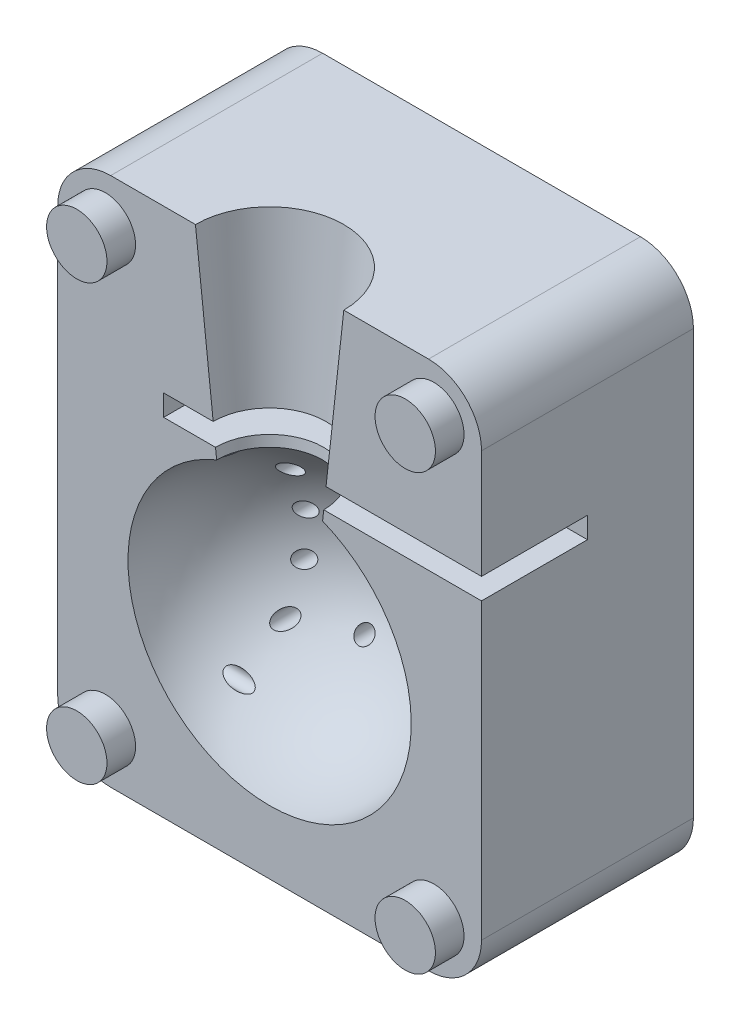
SolidWorks part; units mm, degrees
ref_plane "Alzado" through (0, 0, 0) normal (0, 0, 1) x (1, 0, 0)
ref_plane "Planta" through (0, 0, 0) normal (0, 1, 0) x (1, 0, 0)
ref_plane "Vista lateral" through (0, 0, 0) normal (1, 0, 0) x (0, 0, -1)
sketch "Sketch1" plane through (0, 0, 0) normal (0, 0, 1) x (1, 0, 0)
  line L0 (0, 0) -> (0, 50)
  line L1 (0, 50) -> (-40, 50)
  line L2 (-40, 50) -> (-40, 0)
  line L3 (-40, 0) -> (0, 0)
  dimension "D1" = 40
  dimension "D2" = 50
extrude "Boss-Extrude1" add sketch "Sketch1" against normal blind 20
sketch "Sketch2" plane through (0, 0, 0) normal (0, 0, 1) x (1, 0, 0)
  line L0 (-40, 50) -> (0, 50) construction
  line L1 (-20, 50) -> (-20, 0) construction
  line L2 (-40, 0) -> (0, 0) construction
  line L3 (-20, 32.73) -> (-20, 6)
  arc A0 (-20, 32.73) -> (-20, 6) centre (-20, 19.365) ccw
  dimension "D1" = 26.73
  dimension "D2" = 6
revolve "Cut-Revolve4" cut sketch "Sketch2" angle 360 about L1
sketch "Sketch3" plane through (0, 0, 0) normal (0, 0, 1) x (1, 0, 0)
  line L0 (-40, 50) -> (0, 50) construction
  line L1 (-20, -8.8718) -> (-20, 57.4274) construction
  line L2 (-27, 50) -> (-25, 31.7595)
  line L3 (-27, 50) -> (-20, 50)
  line L4 (-20, 50) -> (-20, 32.73)
  line L5 (-25, 31.7595) -> (-20, 32.73)
  circle A0 centre (-20, 19.365) radius 13.365 construction
  arc A1 (-25, 31.7595) -> (-20, 32.73) centre (-20, 19.365) cw
  dimension "D1" = 7
  dimension "D2" = 5
revolve "Cut-Revolve5" cut sketch "Sketch3" angle 360 about L1
ref_plane "Plane1" through (-20, 0, 0) normal (1, 0, 0) x (0, 0, -1)
sketch "Sketch6" plane through (0, 0, 0) normal (0, 0, 1) x (1, 0, 0)
  line L0 (-40.4401, 40.1066) -> (-40, 50) construction
  line L1 (-40, 50) -> (0, 50) construction
  line L2 (0, 50) -> (0, 0) construction
  line L3 (-20, 44.829) -> (-20, -4.3211) construction
  line L4 (-20, -11) -> (-20, 11) construction
  line L5 (-40, 25) -> (0, 25) construction
  line L6 (-40, 50) -> (-40, 0) construction
  circle A0 centre (-4.5, 45.5) radius 2.85
  circle A1 centre (-35.5, 45.5) radius 2.85
  circle A2 centre (-4.5, 4.5) radius 2.85
  circle A3 centre (-35.5, 4.5) radius 2.85
  dimension "D1" = 4.5
  dimension "D2" = 4.5
  dimension "D3" = 5.7
fillet "Fillet3" radius 5 4 edges at (-40, 0, -10) (0, 0, -10) (0, 50, -10) (-40, 50, -10)
sketch "Sketch10" plane through (0, 0, 0) normal (0, 0, 1) x (1, 0, 0)
  line L0 (0, 34.735) -> (0, 32.735)
  line L1 (-30, 32.735) -> (0, 32.735)
  line L4 (0, 34.735) -> (-30, 34.735)
  line L5 (-30, 34.735) -> (-30, 32.735)
  line L6 (0, 5) -> (0, 45) construction
  circle A1 centre (-20, 19.365) radius 13.37 construction
  arc A2 (-25, 31.7595) -> (-15, 31.7595) centre (-20, 19.365) ccw construction
  dimension "D1" = 26.74
  dimension "D2" = 30
  dimension "D3" = 2
  dimension "D4" = 0
extrude "Cut-Extrude5" cut sketch "Sketch10" against normal blind 10
sketch "Sketch13" plane through (0, 0, 0) normal (0, -1, 0) x (1, 0, 0)
  line L0 (-20, -14.5) -> (-6.5, -14.5)
  line L4 (-33.5, -14.5) -> (-20, -14.5)
  line L5 (-33.5, -16.5) -> (-30, -16.5)
  line L6 (-10, -16.5) -> (-6.5, -16.5)
  line L7 (-33.5, -20) -> (-6.5, -20)
  line L8 (-35, -20) -> (-5, -20) construction
  line L9 (-33.5, -20) -> (-30, -16.5)
  line L11 (-10, -16.5) -> (-6.5, -20)
  line L12 (-6.5, -16.5) -> (-6.5, -14.5)
  line L13 (-33.5, -14.5) -> (-33.5, -16.5)
  dimension "D4" = 5.5
  dimension "D5" = 45
  dimension "D6" = 45
extrude "Cut-Extrude7" cut sketch "Sketch13" against normal blind 30
sketch "Sketch14" plane through (0, 0, -14.5) normal (0, 0, -1) x (-1, 0, 0)
  line L0 (20, 31.7595) -> (20, -3.6539) construction
  line L1 (25, 31.7595) -> (15, 31.7595) construction
  line L2 (35, 0) -> (5, 0) construction
  circle A0 centre (27.5, 25) radius 0.75
  circle A1 centre (22.5, 25) radius 0.75
  circle A2 centre (27.5, 21) radius 0.75
  circle A3 centre (22.5, 21) radius 0.75
  circle A4 centre (27.5, 17) radius 0.75
  circle A5 centre (22.5, 17) radius 0.75
  circle A6 centre (27.5, 13) radius 0.75
  circle A7 centre (22.5, 13) radius 0.75
  circle A8 centre (17.5, 13) radius 0.75
  circle A9 centre (12.5, 13) radius 0.75
  circle A10 centre (17.5, 17) radius 0.75
  circle A11 centre (12.5, 17) radius 0.75
  circle A12 centre (17.5, 21) radius 0.75
  circle A13 centre (12.5, 21) radius 0.75
  circle A14 centre (17.5, 25) radius 0.75
  circle A15 centre (12.5, 25) radius 0.75
  dimension "D1" = 1.5
  dimension "D2" = 7.5
  dimension "D3" = 25
  dimension "D4" = 2
  dimension "D5" = 4
extrude "Cut-Extrude8" cut sketch "Sketch14" against normal up to surface (5.6226 mm away)
sketch "Sketch15" plane through (-40, 0, 0) normal (-1, 0, 0) x (0, 0, 1)
  line L0 (-20, 5) -> (0, 5) construction
  line L1 (0, 45) -> (0, 5) construction
  circle A0 centre (-5, 9.87) radius 0.75
  circle A1 centre (-5, 27.87) radius 0.75
  dimension "D1" = 1.5
  dimension "D2" = 1.5
  dimension "D3" = 18
  dimension "D4" = 4.87
  dimension "D5" = 5
  dimension "D6" = 5
extrude "Cut-Extrude9" cut sketch "Sketch15" against normal up to surface (13.0241 mm away)
sketch "Sketch16" plane through (-40, 0, 0) normal (-1, 0, 0) x (0, 0, 1)
  line L0 (-19.75, 27.87) -> (-7.75, 27.87) construction
  line L1 (0, 45) -> (0, 5) construction
  line L2 (-19.5, 9.87) -> (-7.5, 9.87) construction
  circle A0 centre (-5, 27.87) radius 0.75 construction
  circle A2 centre (-5, 9.87) radius 0.75 construction
  text T0 "Algintate" font "Century Gothic" height in points 7
  text T1 "CaCL2\r\n" font "Century Gothic" height in points 8
  dimension "D1" = 0
  dimension "D2" = 12
  dimension "D3" = 7.75
  dimension "D4" = 0
  dimension "D5" = 12
  dimension "D6" = 7.5
extrude "Cut-Extrude10" cut sketch "Sketch16" against normal blind 1
sketch "Sketch17" plane through (-40, 0, 0) normal (-1, 0, 0) x (0, 0, 1)
  circle A0 centre (-5, 27.87) radius 2.5
  circle A1 centre (-5, 9.87) radius 2.5
  dimension "D1" = 5
  dimension "D2" = 5
extrude "Cut-Extrude11" cut sketch "Sketch17" against normal blind 4
ref_plane "Plane2" through (0, 0, -5) normal (0, 0, 1) x (1, 0, 0)
sketch "Sketch19" plane through (0, 0, -5) normal (0, 0, 1) x (1, 0, 0)
  line L0 (-36, 28.62) -> (-40, 28.62)
  line L1 (-28.2443, 28.62) -> (-36, 28.62) construction
  line L2 (-40, 28.62) -> (-40, 28.87)
  line L3 (-40, 28.87) -> (-37.5, 29.42)
  line L4 (-37.5, 29.42) -> (-37.5, 29.17)
  line L5 (-37.5, 29.17) -> (-36, 29.17)
  line L6 (-36, 29.17) -> (-36, 28.62)
  line L10 (-36, 30.37) -> (-36, 25.37) construction
  line L11 (-36, 27.87) -> (-40.753, 27.87) construction
  line L12 (-36, 18.87) -> (-36, 28.62) construction
  dimension "D1" = 4
  dimension "D3" = 1.5
  dimension "D4" = 1
  dimension "D5" = 1.3
  dimension "D6" = 1.55
revolve "Revolve2" add sketch "Sketch19" angle 360 about L11
ref_plane "Plane3" through (0, 18.87, 0) normal (0, -1, 0) x (-1, 0, 0)
mirror "Mirror1" about plane through (0, 18.87, 0) normal (0, -1, 0) of "Revolve2"
extrude "Boss-Extrude2" add sketch "Sketch6" along normal blind 2.7
